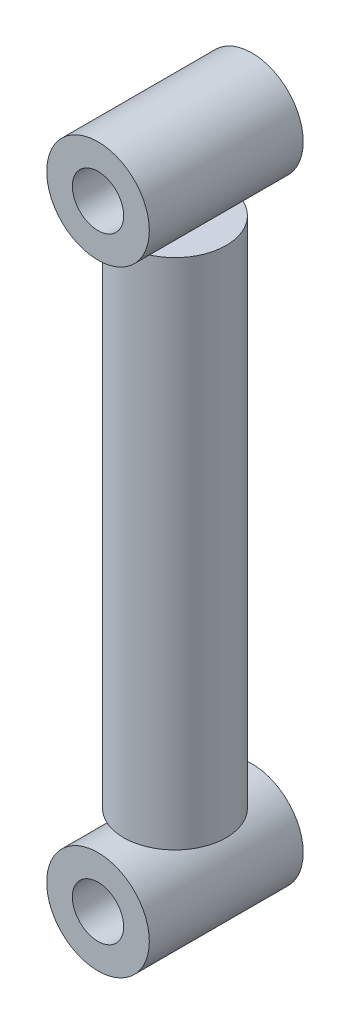
SolidWorks part; units mm, degrees
ref_plane "Front Plane" through (0, 0, 0) normal (0, 0, 1) x (1, 0, 0)
ref_plane "Top Plane" through (0, 0, 0) normal (0, 1, 0) x (1, 0, 0)
ref_plane "Right Plane" through (0, 0, 0) normal (1, 0, 0) x (0, 0, -1)
sketch "Sketch2" plane through (0, 0, 0) normal (0, 1, 0) x (1, 0, 0)
  circle A0 centre (0, 0) radius 25.4
  dimension "D1" = 50.8
extrude "Boss-Extrude1" add sketch "Sketch2" along normal blind 254
sketch "Sketch3" plane through (0, 0, 0) normal (0, 0, 1) x (1, 0, 0)
  line L2 (25.4, 254) -> (-25.4, 254) construction
  circle A0 centre (0, 279.4) radius 25.4
  dimension "D1" = 50.8
extrude "Boss-Extrude2" add sketch "Sketch3" along normal mid plane 76.2 separate body
sketch "Sketch4" plane through (0, 0, 0) normal (0, 0, 1) x (1, 0, 0)
  line L2 (-25.4, 0) -> (25.4, 0) construction
  circle A0 centre (0, -25.4) radius 25.4
  dimension "D1" = 50.8
extrude "Boss-Extrude3" add sketch "Sketch4" along normal mid plane 76.2 separate body
sketch "Sketch5" plane through (0, 0, 38.1) normal (0, 0, 1) x (1, 0, 0)
  circle A0 centre (0, 279.4) radius 12.7
  dimension "D1" = 25.4
extrude "Cut-Extrude1" cut sketch "Sketch5" against normal through all
sketch "Sketch6" plane through (0, 0, 38.1) normal (0, 0, 1) x (1, 0, 0)
  circle A0 centre (0, -25.4) radius 12.7
  dimension "D1" = 25.4
extrude "Cut-Extrude2" cut sketch "Sketch6" against normal through all
